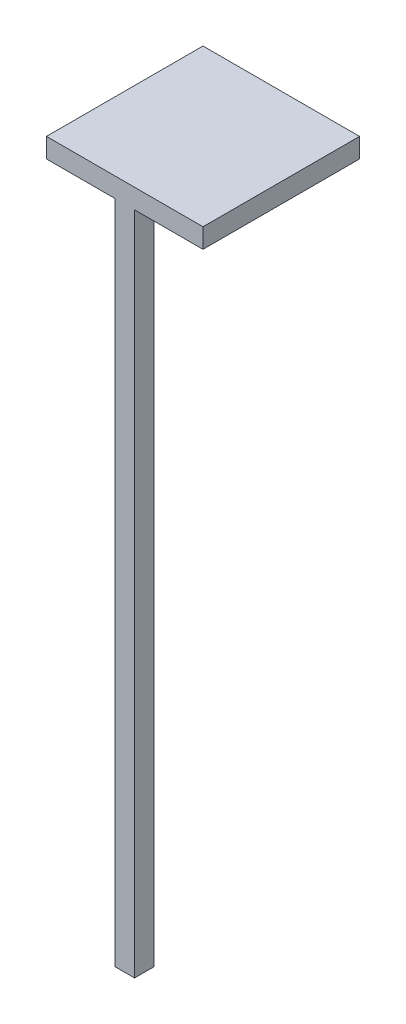
SolidWorks part; units mm, degrees
ref_plane "Face" through (0, 0, 0) normal (0, 0, 1) x (1, 0, 0)
ref_plane "Dessus" through (0, 0, 0) normal (0, 1, 0) x (1, 0, 0)
ref_plane "Droite" through (0, 0, 0) normal (1, 0, 0) x (0, 0, -1)
sketch "Esquisse1" plane through (0, 0, 0) normal (0, 1, 0) x (1, 0, 0)
  line L1 (0, 0) -> (10, 0)
  line L2 (0, 0) -> (0, 10)
  line L3 (0, 10) -> (10, 10)
  line L4 (10, 0) -> (10, 10)
  dimension "D1" = 10
  dimension "D2" = 10
extrude "Extrusion1" add sketch "Esquisse1" along normal blind 340
sketch "Esquisse2" plane through (0, 340, 0) normal (0, 1, 0) x (1, 0, 0)
  line L0 (0, 10) -> (0, 0) construction
  line L1 (-35, 0) -> (45, 0)
  line L2 (-35, 0) -> (-35, 80)
  line L3 (-35, 80) -> (45, 80)
  line L4 (45, 0) -> (45, 80)
  line L5 (0, 0) -> (10, 0) construction
  dimension "D1" = 80
  dimension "D2" = 80
  dimension "D3" = 35
extrude "Extrusion2" add sketch "Esquisse2" along normal blind 10
